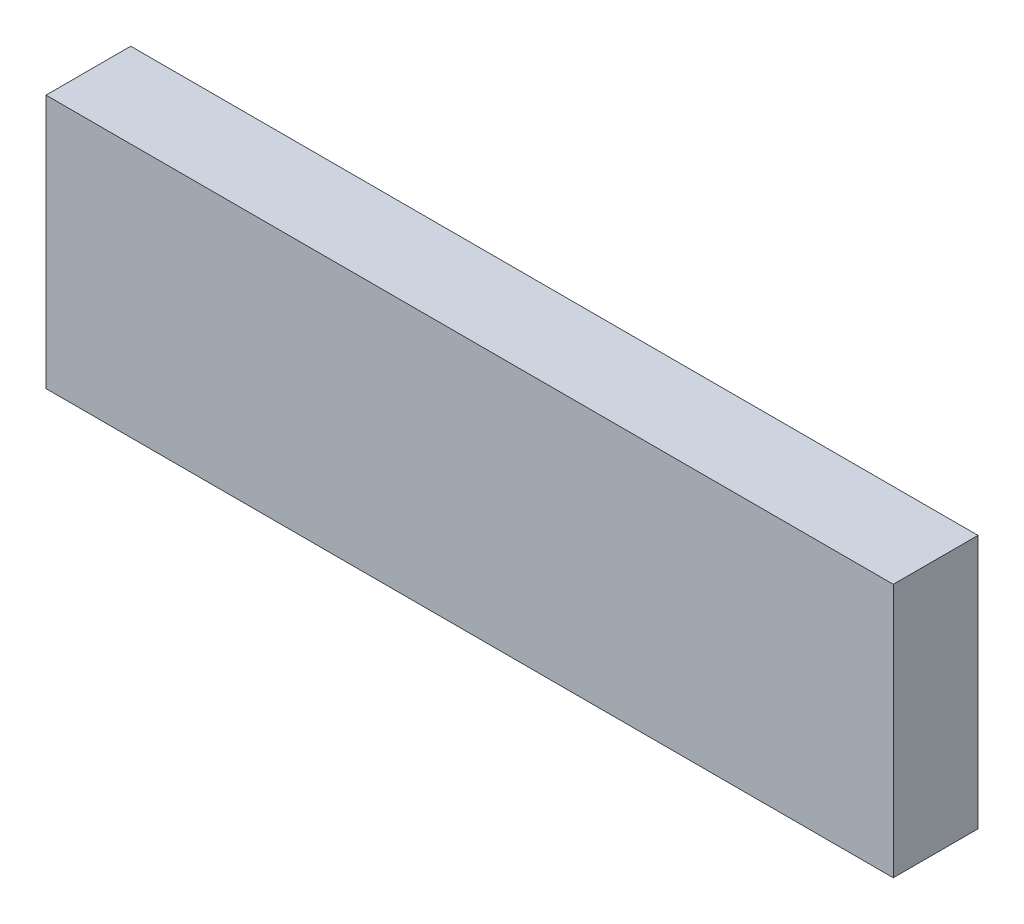
SolidWorks part; units mm, degrees
ref_plane "Front Plane" through (0, 0, 0) normal (0, 0, 1) x (1, 0, 0)
ref_plane "Top Plane" through (0, 0, 0) normal (0, 1, 0) x (1, 0, 0)
ref_plane "Right Plane" through (0, 0, 0) normal (1, 0, 0) x (0, 0, -1)
sketch "Sketch1" plane through (0, 0, 0) normal (0, 0, 1) x (1, 0, 0)
  line L1 (-88.3486, 42.544) -> (11.6514, 42.544)
  line L2 (-88.3486, 42.544) -> (-88.3486, 12.544)
  line L3 (-88.3486, 12.544) -> (11.6514, 12.544)
  line L4 (11.6514, 42.544) -> (11.6514, 12.544)
  dimension "D1" = 100
  dimension "D2" = 30
extrude "Boss-Extrude1" add sketch "Sketch1" along normal blind 10
